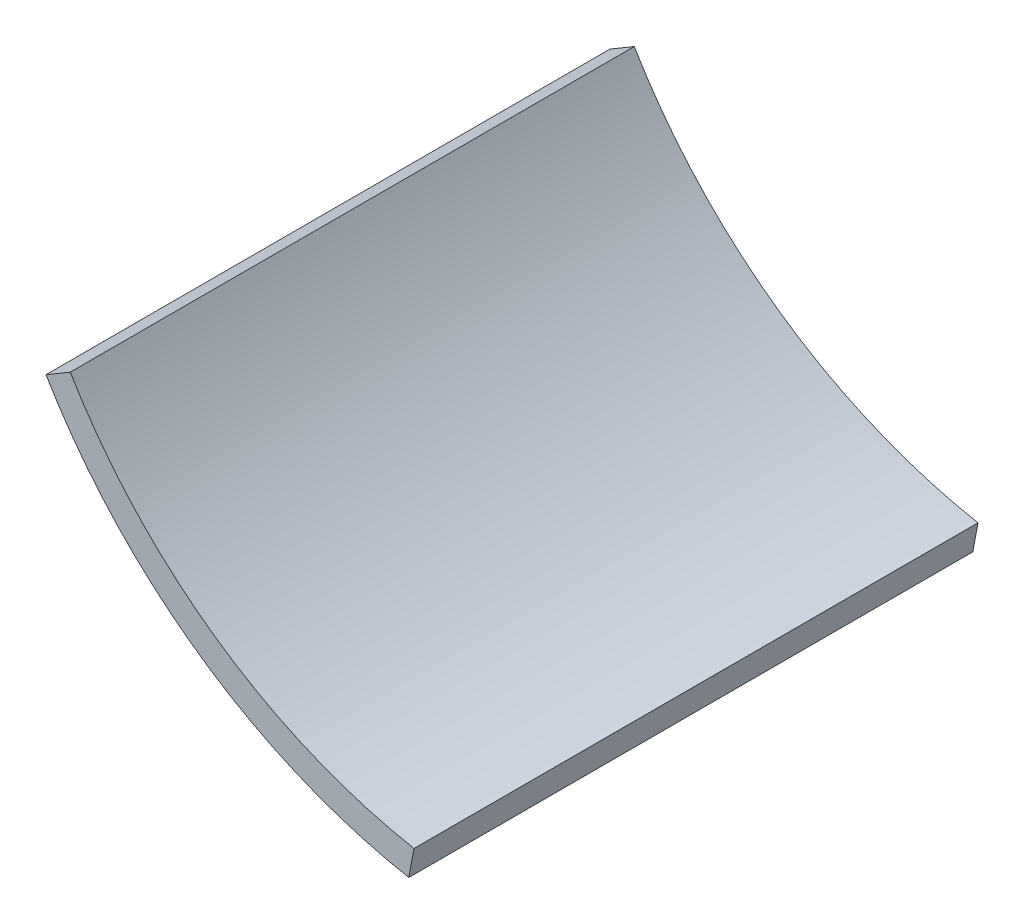
SolidWorks part; units mm, degrees
material "ALUMINUM 6061-T6"
ref_plane "Front Plane" through (0, 0, 0) normal (0, 0, 1) x (1, 0, 0)
ref_plane "Top Plane" through (0, 0, 0) normal (0, 1, 0) x (1, 0, 0)
ref_plane "Right Plane" through (0, 0, 0) normal (1, 0, 0) x (0, 0, -1)
sketch "Sketch4" plane through (0, 0, 0) normal (0, 0, 1) x (1, 0, 0)
  circle A0 centre (0, 0) radius 120.65
  circle A1 centre (0, 0) radius 114.3
  dimension "D1" = 241.3
  dimension "D2" = 228.6
extrude "Boss-Extrude3" add sketch "Sketch4" along normal mid plane 127
sketch "Sketch6" plane through (0, 0, 63.5) normal (0, 0, 1) x (1, 0, 0)
  line L0 (-23.6883, -126.7686) -> (0, 0)
  line L1 (0, 0) -> (-123.6101, -73.075)
  line L2 (-123.6101, -73.075) -> (-158.0659, 116.719)
  line L3 (-158.0659, 116.719) -> (139.4023, 136.2439)
  line L4 (139.4023, 136.2439) -> (181.3235, -82.2632)
  line L5 (181.3235, -82.2632) -> (155.4922, -108.8903)
  line L6 (155.4922, -108.8903) -> (-23.6883, -126.7686)
extrude "Cut-Extrude1" cut sketch "Sketch6" against normal blind 127
